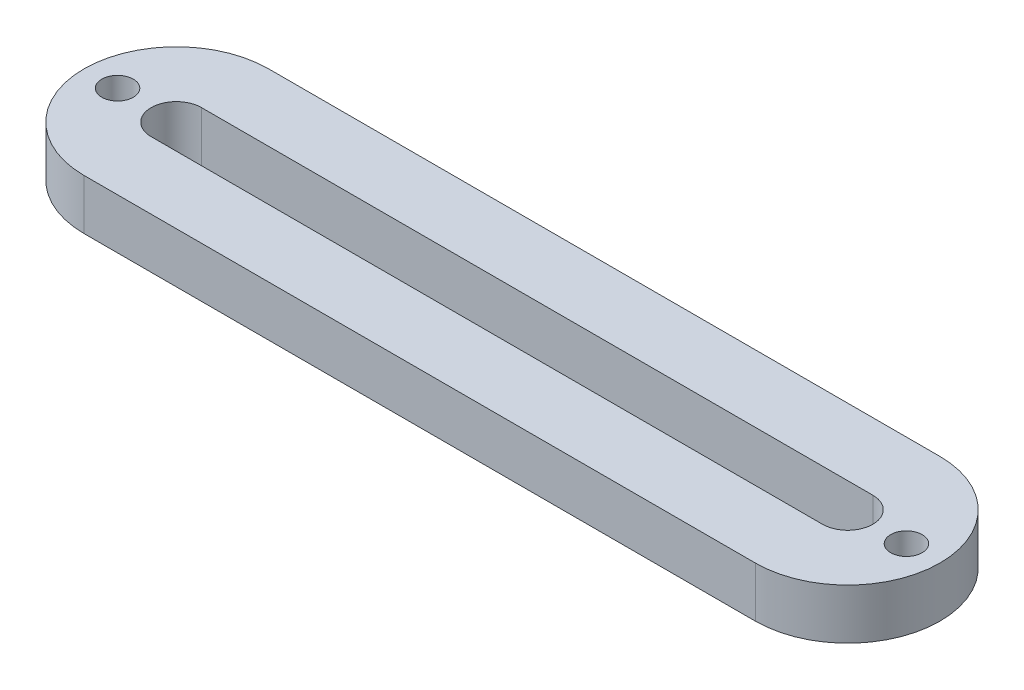
SolidWorks part; units mm, degrees
ref_plane "Front" through (0, 0, 0) normal (0, 0, 1) x (1, 0, 0)
ref_plane "Top" through (0, 0, 0) normal (0, 1, 0) x (1, 0, 0)
ref_plane "Right" through (0, 0, 0) normal (1, 0, 0) x (0, 0, -1)
sketch "Croquis1" plane through (0, 0, 0) normal (0, 1, 0) x (1, 0, 0)
  line L0 (-40, 0) -> (40, 0) construction
  line L1 (-40, 3) -> (40, 3)
  line L2 (-40, -3) -> (40, -3)
  line L3 (-40, 0) -> (40, 0) construction
  line L4 (-40, 11) -> (40, 11)
  line L5 (-40, -11) -> (40, -11)
  line L6 (-43, 0) -> (-51, 0) construction
  line L7 (0, 11) -> (0, -11) construction
  arc A0 (-40, 3) -> (-40, -3) centre (-40, 0) ccw
  arc A1 (40, -3) -> (40, 3) centre (40, 0) ccw
  arc A2 (-40, 11) -> (-40, -11) centre (-40, 0) ccw
  arc A3 (40, -11) -> (40, 11) centre (40, 0) ccw
  circle A4 centre (-47, 0) radius 1.875
  circle A5 centre (47, 0) radius 1.875
  point P3 (0, 0)
  point P8 (0, 0)
  dimension "D2" = 3
  dimension "D4" = 3.75
  dimension "D1" = 80
  dimension "D3" = 8
extrude "Saliente-Extruir1" add sketch "Croquis1" along normal blind 6
sketch "Croquis2" plane through (0, 0, 0) normal (0, 1, 0) x (1, 0, 0)
  line L0 (-47, 0) -> (47, 0) construction
  line L2 (-45.4, -2.7713) -> (-43.8, 0)
  line L3 (-43.8, 0) -> (-45.4, 2.7713)
  line L4 (-45.4, 2.7713) -> (-48.6, 2.7713)
  line L5 (-48.6, 2.7713) -> (-50.2, 0)
  line L6 (-50.2, 0) -> (-48.6, -2.7713)
  line L7 (-48.6, -2.7713) -> (-45.4, -2.7713)
  line L9 (0, 0) -> (0, -3) construction
  line L10 (51, 0) -> (43, 0) construction
  line L12 (48.6, -2.7713) -> (45.4, -2.7713)
  line L13 (-51, 0) -> (-43, 0) construction
  line L14 (50.2, 0) -> (48.6, -2.7713)
  line L15 (48.6, 2.7713) -> (50.2, 0)
  line L16 (-40, -11) -> (40, -11)
  line L17 (40, 11) -> (-40, 11)
  line L18 (-40, -11) -> (40, -11)
  line L19 (40, 11) -> (-40, 11)
  line L20 (45.4, 2.7713) -> (48.6, 2.7713)
  line L21 (43.8, 0) -> (45.4, 2.7713)
  line L22 (-40, -3) -> (40, -3)
  line L23 (40, 3) -> (-40, 3)
  line L24 (-40, -3) -> (40, -3)
  line L25 (40, 3) -> (-40, 3)
  line L26 (45.4, -2.7713) -> (43.8, 0)
  circle A0 centre (-47, 0) radius 2.7713 construction
  circle A1 centre (47, 0) radius 2.7713 construction
  arc A2 (-40, 11) -> (-40, -11) centre (-40, 0) ccw construction
  arc A3 (-40, 3) -> (-40, -3) centre (-40, 0) ccw construction
  arc A6 (-40, 11) -> (-40, -11) centre (-40, 0) ccw
  arc A7 (40, -11) -> (40, 11) centre (40, 0) ccw
  arc A8 (-40, 11) -> (-40, -11) centre (-40, 0) ccw
  arc A9 (40, -11) -> (40, 11) centre (40, 0) ccw
  arc A12 (-40, 3) -> (-40, -3) centre (-40, 0) ccw
  arc A13 (40, -3) -> (40, 3) centre (40, 0) ccw
  arc A14 (-40, 3) -> (-40, -3) centre (-40, 0) ccw
  arc A15 (40, -3) -> (40, 3) centre (40, 0) ccw
  point P9 (0, 0)
  point P17 (-47, 0)
  dimension "D1" = 3.2
  dimension "D2" = 0
  dimension "D3" = 0
extrude "Cortar-Extruir1" [suppressed] cut sketch "Croquis2" along normal blind 6 contours L26 L12 L14 L15 L20 L21 | L4 L5 L6 L7 L2 L3
sketch "Croquis5" [suppressed] plane through (0, 6, 0) normal (0, -1, 0) x (1, 0, 0)
  line L0 (-51.6, 2.7713) -> (-48.4, -2.7713) construction
  line L1 (0, 0) -> (0, -4.4647) construction
  line L2 (40, 6) -> (-40, 6)
  line L3 (-40, -6) -> (40, -6)
  line L4 (40, 6) -> (-40, 6)
  line L5 (-40, -6) -> (40, -6)
  line L6 (-46.8, 0) -> (-48.4, 2.7713)
  line L7 (-48.4, -2.7713) -> (-46.8, 0)
  line L8 (-51.6, -2.7713) -> (-48.4, -2.7713)
  line L9 (-53.2, 0) -> (-51.6, -2.7713)
  line L10 (-51.6, 2.7713) -> (-53.2, 0)
  line L11 (-48.4, 2.7713) -> (-51.6, 2.7713)
  line L12 (-46.8, 0) -> (-48.4, 2.7713)
  line L13 (-48.4, -2.7713) -> (-46.8, 0)
  line L14 (-51.6, -2.7713) -> (-48.4, -2.7713)
  line L15 (-53.2, 0) -> (-51.6, -2.7713)
  line L16 (-51.6, 2.7713) -> (-53.2, 0)
  line L17 (-48.4, 2.7713) -> (-51.6, 2.7713)
  line L18 (40, 14) -> (-40, 14)
  line L19 (-40, -14) -> (40, -14)
  line L20 (40, 14) -> (-40, 14)
  line L21 (-40, -14) -> (40, -14)
  line L26 (51.6, 2.7713) -> (48.4, 2.7713)
  line L27 (53.2, 0) -> (51.6, 2.7713)
  line L28 (51.6, -2.7713) -> (53.2, 0)
  line L29 (48.4, -2.7713) -> (51.6, -2.7713)
  line L30 (46.8, 0) -> (48.4, -2.7713)
  line L31 (48.4, 2.7713) -> (46.8, 0)
  line L32 (51.6, 2.7713) -> (48.4, 2.7713)
  line L33 (53.2, 0) -> (51.6, 2.7713)
  line L34 (51.6, -2.7713) -> (53.2, 0)
  line L35 (48.4, -2.7713) -> (51.6, -2.7713)
  line L36 (46.8, 0) -> (48.4, -2.7713)
  line L37 (48.4, 2.7713) -> (46.8, 0)
  circle A0 centre (-50, 0) radius 1.875
  circle A1 centre (50, 0) radius 1.875
  arc A2 (40, -6) -> (40, 6) centre (40, 0) ccw
  arc A3 (-40, 6) -> (-40, -6) centre (-40, 0) ccw
  arc A4 (40, -6) -> (40, 6) centre (40, 0) ccw
  arc A5 (-40, 6) -> (-40, -6) centre (-40, 0) ccw
  arc A6 (40, -14) -> (40, 14) centre (40, 0) ccw
  arc A7 (-40, 14) -> (-40, -14) centre (-40, 0) ccw
  arc A8 (40, -14) -> (40, 14) centre (40, 0) ccw
  arc A9 (-40, 14) -> (-40, -14) centre (-40, 0) ccw
  dimension "D5" = 3.75
  dimension "D1" = 0
  dimension "D2" = 0
  dimension "D3" = 0
  dimension "D4" = 0
extrude "Cortar-Extruir2" [suppressed] cut sketch "Croquis5" against normal through all both and the other way through all contours A0 | A1
sketch "Croquis6" [suppressed] plane through (0, 8, 0) normal (0, 1, 0) x (1, 0, 0)
  line L0 (-40, 14) -> (-40, -14)
  line L1 (40, 14) -> (40, -14)
  line L2 (-40, -14) -> (40, -14)
  line L3 (40, 14) -> (-40, 14)
  line L4 (-40, -14) -> (40, -14)
  line L5 (40, 14) -> (-40, 14)
  line L10 (-40, -6) -> (40, -6)
  line L11 (40, 6) -> (-40, 6)
  line L12 (-40, -6) -> (40, -6)
  line L13 (40, 6) -> (-40, 6)
  arc A2 (-40, 14) -> (-40, -14) centre (-40, 0) ccw
  arc A3 (40, -14) -> (40, 14) centre (40, 0) ccw
  arc A4 (-40, 14) -> (-40, -14) centre (-40, 0) ccw
  arc A5 (40, -14) -> (40, 14) centre (40, 0) ccw
  circle A9 centre (-50, 0) radius 1.875
  arc A10 (-40, 6) -> (-40, -6) centre (-40, 0) ccw
  arc A11 (40, -6) -> (40, 6) centre (40, 0) ccw
  arc A12 (-40, 6) -> (-40, -6) centre (-40, 0) ccw
  arc A13 (40, -6) -> (40, 6) centre (40, 0) ccw
  circle A14 centre (-50, 0) radius 1.875
  circle A15 centre (50, 0) radius 1.875
  circle A16 centre (50, 0) radius 1.875
  line M14 (-40, -14) -> (40, -14)
  line M16 (40, 14) -> (-40, 14)
  line M17 (40, -6) -> (-40, -6)
  line M19 (-40, 6) -> (40, 6)
  dimension "D2" = 0
  dimension "D1" = 0
  dimension "D3" = 0
  dimension "D4" = 0
extrude "Saliente-Extruir4" [suppressed] add sketch "Croquis6" along normal blind 1 contours L1 L0 M16 M19 | L1 L0 M17 M14
